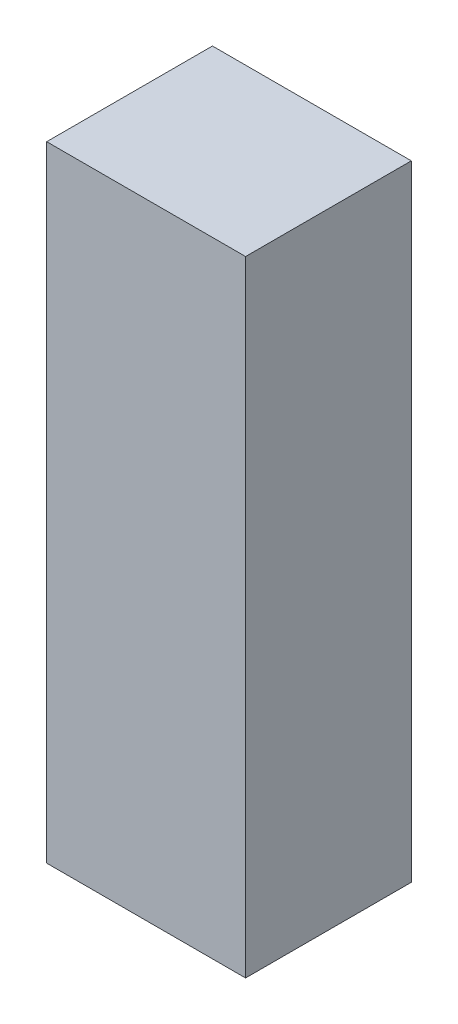
SolidWorks part; units mm, degrees
material "1023 al carbonio, lamiera (SS)"
ref_plane "Piano frontale" through (0, 0, 0) normal (0, 0, 1) x (1, 0, 0)
ref_plane "Piano superiore" through (0, 0, 0) normal (0, 1, 0) x (1, 0, 0)
ref_plane "Piano destro" through (0, 0, 0) normal (1, 0, 0) x (0, 0, -1)
sketch "Schizzo1" plane through (0, 0, 0) normal (0, 0, 1) x (1, 0, 0)
  line L0 (6, 37.699) -> (6, 0) construction
  line L1 (0, 0) -> (12, 0)
  line L2 (0, 0) -> (0, 37.699)
  line L3 (0, 37.699) -> (12, 37.699)
  line L4 (12, 0) -> (12, 37.699)
  dimension "D1" = 37.699
  dimension "D2" = 12
extrude "Estrusione-Estrusione1" add sketch "Schizzo1" along normal blind 10
